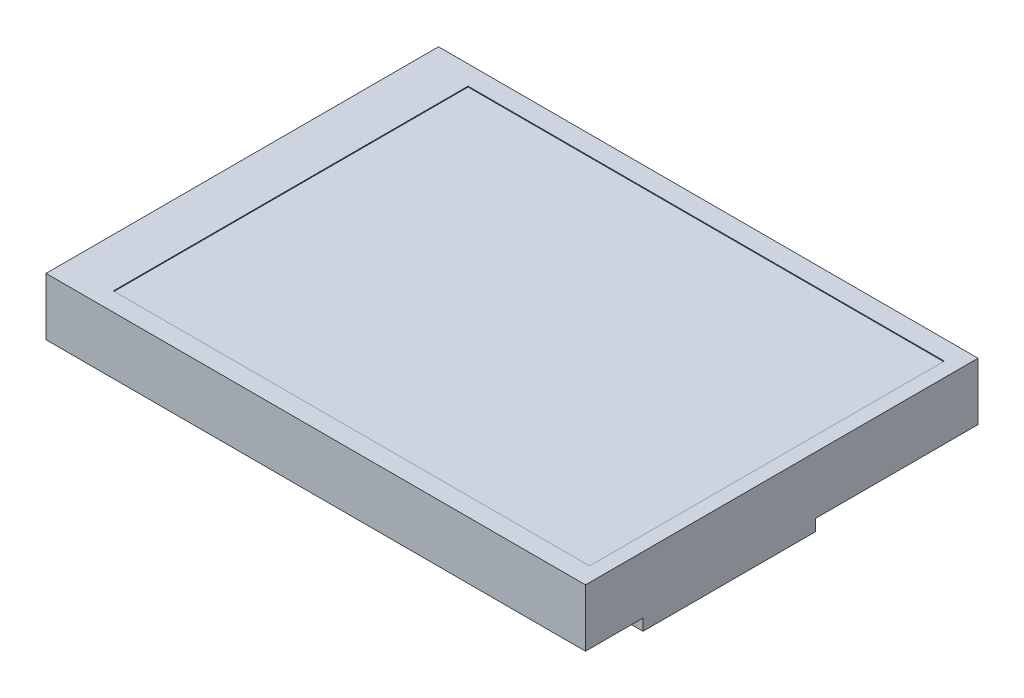
SolidWorks part; units mm, degrees
ref_plane "Front Plane" through (0, 0, 0) normal (0, 0, 1) x (1, 0, 0)
ref_plane "Top Plane" through (0, 0, 0) normal (0, 1, 0) x (1, 0, 0)
ref_plane "Right Plane" through (0, 0, 0) normal (1, 0, 0) x (0, 0, -1)
sketch "Sketch1" plane through (0, 0, 0) normal (0, 1, 0) x (1, 0, 0)
  line L1 (0, 0) -> (65.7, 0)
  line L2 (0, 0) -> (0, 47.8)
  line L3 (0, 47.8) -> (65.7, 47.8)
  line L4 (65.7, 0) -> (65.7, 47.8)
  dimension "D1" = 47.8
  dimension "D2" = 65.7
extrude "Boss-Extrude1" add sketch "Sketch1" along normal blind 7
sketch "Sketch2" plane through (0, 7, 0) normal (0, 1, 0) x (1, 0, 0)
  line L1 (5.95, 45.45) -> (63.95, 45.45)
  line L2 (5.95, 45.45) -> (5.95, 2.25)
  line L3 (5.95, 2.25) -> (63.95, 2.25)
  line L4 (63.95, 45.45) -> (63.95, 2.25)
  line L5 (65.7, 47.8) -> (0, 47.8) construction
  line L6 (0, 0) -> (65.7, 0) construction
  line L9 (65.7, 0) -> (65.7, 47.8) construction
  dimension "D2" = 2.35
  dimension "D3" = 2.25
  dimension "D4" = 1.75
  dimension "D5" = 58
extrude "Cut-Extrude1" cut sketch "Sketch2" against normal blind 0.1
sketch "Sketch3" plane through (0, 0, 0) normal (0, -1, 0) x (1, 0, 0)
  line L1 (52.7, -7) -> (65.7, -7)
  line L2 (52.7, -7) -> (52.7, -28)
  line L3 (52.7, -28) -> (65.7, -28)
  line L4 (65.7, -7) -> (65.7, -28)
  line L5 (0, 0) -> (65.7, 0) construction
  line L6 (65.7, 0) -> (65.7, -47.8) construction
  dimension "D1" = 13
  dimension "D2" = 21
  dimension "D3" = 7
extrude "Boss-Extrude2" add sketch "Sketch3" along normal blind 1.4
sketch "Sketch4" plane through (0, 0, 0) normal (0, -1, 0) x (1, 0, 0)
  line L0 (0, 0) -> (65.7, 0) construction
  line L1 (25, -3.5) -> (30.5, -3.5)
  line L2 (25, -3.5) -> (25, -12)
  line L3 (25, -12) -> (30.5, -12)
  line L4 (30.5, -3.5) -> (30.5, -12)
  line L6 (0, -47.8) -> (0, 0) construction
  dimension "D1" = 5.5
  dimension "D2" = 8.5
  dimension "D3" = 3.5
  dimension "D4" = 25
extrude "Boss-Extrude3" add sketch "Sketch4" along normal blind 2.1
sketch "Sketch5" plane through (0, 0, 0) normal (0, -1, 0) x (1, 0, 0)
  line L0 (25, -12) -> (30.5, -12) construction
  line L1 (29.7, -16) -> (25.7, -16)
  line L2 (29.7, -16) -> (29.7, -31)
  line L3 (29.7, -31) -> (25.7, -31)
  line L4 (25.7, -16) -> (25.7, -31)
  line L8 (65.7, -28) -> (65.7, -47.8) construction
  dimension "D1" = 4
  dimension "D2" = 15
  dimension "D3" = 4
  dimension "D4" = 36
extrude "Boss-Extrude4" add sketch "Sketch5" along normal blind 1.3
sketch "Sketch6" plane through (0, 0, 0) normal (0, -1, 0) x (-1, 0, 0)
  line L0 (-65.7, 0) -> (-65.7, 7) construction
  line L1 (-7.7, 41.3) -> (-58.7, 41.3)
  line L2 (-7.7, 41.3) -> (-7.7, 46.3)
  line L3 (-7.7, 46.3) -> (-58.7, 46.3)
  line L4 (-58.7, 41.3) -> (-58.7, 46.3)
  line L5 (-65.7, 47.8) -> (0, 47.8) construction
  dimension "D1" = 51
  dimension "D2" = 7
  dimension "D3" = 5
  dimension "D4" = 1.5
extrude "Boss-Extrude5" add sketch "Sketch6" along normal blind 4
